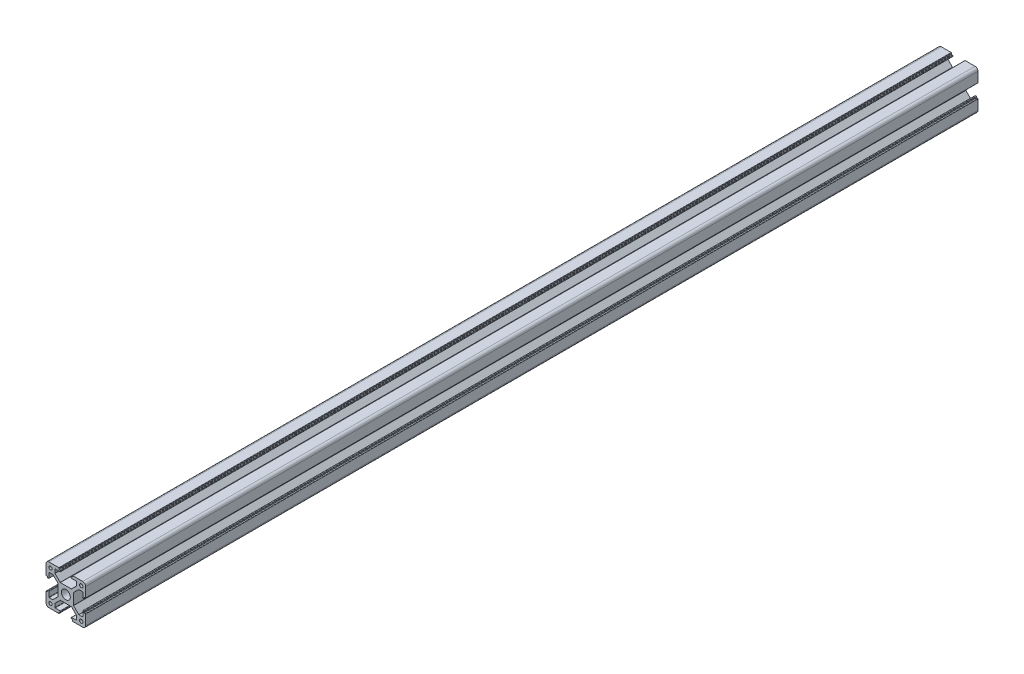
SolidWorks part; units mm, degrees
material "6063-T5"
ref_plane "Alzado" through (0, 0, 0) normal (0, 0, 1) x (1, 0, 0)
ref_plane "Planta" through (0, 0, 0) normal (0, 1, 0) x (1, 0, 0)
ref_plane "Vista lateral" through (0, 0, 0) normal (1, 0, 0) x (0, 0, -1)
sketch "Croquis1" plane through (0, 0, 0) normal (0, 0, 1) x (1, 0, 0)
  line L0 (0, 53.0989) -> (0, -48.4513) construction
  line L1 (-45.0818, 0) -> (46.476, 0) construction
  line L2 (-4.1615, 5.8) -> (4.1615, 5.8)
  line L3 (4.3029, 5.8586) -> (8.1914, 9.7471)
  line L4 (8.25, 9.8885) -> (8.25, 12.6)
  line L5 (8.05, 12.8) -> (4.3, 12.8)
  line L6 (4.1, 13) -> (4.1, 13.7)
  line L7 (4.3, 13.9) -> (4.9, 13.9)
  line L8 (5.1, 14.1) -> (5.1, 14.8)
  line L9 (5.3, 15) -> (12.8, 15)
  line L10 (0, 0) -> (45.9185, 45.9185) construction
  line L11 (15, 5.3) -> (15, 12.8)
  line L12 (13.9, 5.1) -> (14.8, 5.1)
  line L13 (13.9, 4.3) -> (13.9, 5.1)
  line L14 (13, 4.1) -> (13.7, 4.1)
  line L15 (12.8, 8.05) -> (12.8, 4.3)
  line L16 (9.8885, 8.25) -> (12.6, 8.25)
  line L17 (5.8586, 4.3029) -> (9.7471, 8.1914)
  line L18 (5.8, -4.1615) -> (5.8, 4.1615)
  line L19 (5.8586, -4.3029) -> (9.7471, -8.1914)
  line L20 (9.8885, -8.25) -> (12.6, -8.25)
  line L21 (12.8, -8.05) -> (12.8, -4.3)
  line L22 (13, -4.1) -> (13.7, -4.1)
  line L23 (13.9, -4.3) -> (13.9, -5.1)
  line L24 (13.9, -5.1) -> (14.8, -5.1)
  line L25 (15, -5.3) -> (15, -12.8)
  line L26 (5.3, -15) -> (12.8, -15)
  line L27 (5.1, -14.1) -> (5.1, -14.8)
  line L28 (4.3, -13.9) -> (4.9, -13.9)
  line L29 (4.1, -13) -> (4.1, -13.7)
  line L30 (8.05, -12.8) -> (4.3, -12.8)
  line L31 (8.25, -9.8885) -> (8.25, -12.6)
  line L32 (4.3029, -5.8586) -> (8.1914, -9.7471)
  line L33 (-4.1615, -5.8) -> (4.1615, -5.8)
  line L64 (-4.3029, -5.8586) -> (-8.1914, -9.7471)
  line L65 (-8.25, -9.8885) -> (-8.25, -12.6)
  line L66 (-8.05, -12.8) -> (-4.3, -12.8)
  line L67 (-4.1, -13) -> (-4.1, -13.7)
  line L68 (-4.3, -13.9) -> (-4.9, -13.9)
  line L69 (-5.1, -14.1) -> (-5.1, -14.8)
  line L70 (-5.3, -15) -> (-12.8, -15)
  line L71 (-15, -5.3) -> (-15, -12.8)
  line L72 (-13.9, -5.1) -> (-14.8, -5.1)
  line L73 (-13.9, -4.3) -> (-13.9, -5.1)
  line L74 (-13, -4.1) -> (-13.7, -4.1)
  line L75 (-12.8, -8.05) -> (-12.8, -4.3)
  line L76 (-9.8885, -8.25) -> (-12.6, -8.25)
  line L77 (-5.8586, -4.3029) -> (-9.7471, -8.1914)
  line L78 (-5.8586, 4.3029) -> (-9.7471, 8.1914)
  line L79 (-9.8885, 8.25) -> (-12.6, 8.25)
  line L80 (-12.8, 8.05) -> (-12.8, 4.3)
  line L81 (-13, 4.1) -> (-13.7, 4.1)
  line L82 (-13.9, 4.3) -> (-13.9, 5.1)
  line L83 (-13.9, 5.1) -> (-14.8, 5.1)
  line L84 (-15, 5.3) -> (-15, 12.8)
  line L85 (-5.3, 15) -> (-12.8, 15)
  line L86 (-5.1, 14.1) -> (-5.1, 14.8)
  line L87 (-4.3, 13.9) -> (-4.9, 13.9)
  line L88 (-4.1, 13) -> (-4.1, 13.7)
  line L89 (-8.05, 12.8) -> (-4.3, 12.8)
  line L90 (-8.25, 9.8885) -> (-8.25, 12.6)
  line L91 (-4.3029, 5.8586) -> (-8.1914, 9.7471)
  line L106 (-5.8, -4.1615) -> (-5.8, 4.1615)
  arc A0 (12.8, 15) -> (15, 12.8) centre (12.8, 12.8) cw
  arc A1 (5.1, 14.8) -> (5.3, 15) centre (5.3, 14.8) cw
  arc A2 (4.9, 13.9) -> (5.1, 14.1) centre (4.9, 14.1) ccw
  arc A3 (4.1, 13.7) -> (4.3, 13.9) centre (4.3, 13.7) cw
  arc A4 (4.3, 12.8) -> (4.1, 13) centre (4.3, 13) cw
  arc A5 (8.25, 12.6) -> (8.05, 12.8) centre (8.05, 12.6) ccw
  arc A6 (4.1615, 5.8) -> (4.3029, 5.8586) centre (4.1615, 6) ccw
  arc A7 (8.1914, 9.7471) -> (8.25, 9.8885) centre (8.05, 9.8885) ccw
  arc A8 (13, 4.1) -> (12.8, 4.3) centre (13, 4.3) cw
  arc A9 (5.8586, 4.3029) -> (5.8, 4.1615) centre (6, 4.1615) ccw
  arc A10 (9.8885, 8.25) -> (9.7471, 8.1914) centre (9.8885, 8.05) ccw
  arc A11 (12.8, 8.05) -> (12.6, 8.25) centre (12.6, 8.05) ccw
  arc A12 (13.9, 4.3) -> (13.7, 4.1) centre (13.7, 4.3) cw
  arc A13 (15, 5.3) -> (14.8, 5.1) centre (14.8, 5.3) cw
  arc A16 (15, -5.3) -> (14.8, -5.1) centre (14.8, -5.3) ccw
  arc A17 (13.9, -4.3) -> (13.7, -4.1) centre (13.7, -4.3) ccw
  arc A18 (12.8, -8.05) -> (12.6, -8.25) centre (12.6, -8.05) cw
  arc A19 (9.8885, -8.25) -> (9.7471, -8.1914) centre (9.8885, -8.05) cw
  arc A20 (5.8586, -4.3029) -> (5.8, -4.1615) centre (6, -4.1615) cw
  arc A21 (13, -4.1) -> (12.8, -4.3) centre (13, -4.3) ccw
  arc A22 (8.1914, -9.7471) -> (8.25, -9.8885) centre (8.05, -9.8885) cw
  arc A23 (4.1615, -5.8) -> (4.3029, -5.8586) centre (4.1615, -6) cw
  arc A24 (8.25, -12.6) -> (8.05, -12.8) centre (8.05, -12.6) cw
  arc A25 (4.3, -12.8) -> (4.1, -13) centre (4.3, -13) ccw
  arc A26 (4.1, -13.7) -> (4.3, -13.9) centre (4.3, -13.7) ccw
  arc A27 (4.9, -13.9) -> (5.1, -14.1) centre (4.9, -14.1) cw
  arc A28 (5.1, -14.8) -> (5.3, -15) centre (5.3, -14.8) ccw
  arc A29 (12.8, -15) -> (15, -12.8) centre (12.8, -12.8) ccw
  circle A44 centre (11.625, 11.625) radius 1.25
  circle A45 centre (11.625, -11.625) radius 1.25
  arc A60 (-12.8, -15) -> (-15, -12.8) centre (-12.8, -12.8) cw
  arc A61 (-5.1, -14.8) -> (-5.3, -15) centre (-5.3, -14.8) cw
  arc A62 (-4.9, -13.9) -> (-5.1, -14.1) centre (-4.9, -14.1) ccw
  arc A63 (-4.1, -13.7) -> (-4.3, -13.9) centre (-4.3, -13.7) cw
  arc A64 (-4.3, -12.8) -> (-4.1, -13) centre (-4.3, -13) cw
  arc A65 (-8.25, -12.6) -> (-8.05, -12.8) centre (-8.05, -12.6) ccw
  arc A66 (-4.1615, -5.8) -> (-4.3029, -5.8586) centre (-4.1615, -6) ccw
  arc A67 (-8.1914, -9.7471) -> (-8.25, -9.8885) centre (-8.05, -9.8885) ccw
  arc A68 (-13, -4.1) -> (-12.8, -4.3) centre (-13, -4.3) cw
  arc A69 (-5.8586, -4.3029) -> (-5.8, -4.1615) centre (-6, -4.1615) ccw
  arc A70 (-9.8885, -8.25) -> (-9.7471, -8.1914) centre (-9.8885, -8.05) ccw
  arc A71 (-12.8, -8.05) -> (-12.6, -8.25) centre (-12.6, -8.05) ccw
  arc A72 (-13.9, -4.3) -> (-13.7, -4.1) centre (-13.7, -4.3) cw
  arc A73 (-15, -5.3) -> (-14.8, -5.1) centre (-14.8, -5.3) cw
  arc A76 (-15, 5.3) -> (-14.8, 5.1) centre (-14.8, 5.3) ccw
  arc A77 (-13.9, 4.3) -> (-13.7, 4.1) centre (-13.7, 4.3) ccw
  arc A78 (-12.8, 8.05) -> (-12.6, 8.25) centre (-12.6, 8.05) cw
  arc A79 (-9.8885, 8.25) -> (-9.7471, 8.1914) centre (-9.8885, 8.05) cw
  arc A80 (-5.8586, 4.3029) -> (-5.8, 4.1615) centre (-6, 4.1615) cw
  arc A81 (-13, 4.1) -> (-12.8, 4.3) centre (-13, 4.3) ccw
  arc A82 (-8.1914, 9.7471) -> (-8.25, 9.8885) centre (-8.05, 9.8885) cw
  arc A83 (-4.1615, 5.8) -> (-4.3029, 5.8586) centre (-4.1615, 6) cw
  arc A84 (-8.25, 12.6) -> (-8.05, 12.8) centre (-8.05, 12.6) cw
  arc A85 (-4.3, 12.8) -> (-4.1, 13) centre (-4.3, 13) ccw
  arc A86 (-4.1, 13.7) -> (-4.3, 13.9) centre (-4.3, 13.7) ccw
  arc A87 (-4.9, 13.9) -> (-5.1, 14.1) centre (-4.9, 14.1) cw
  arc A88 (-5.1, 14.8) -> (-5.3, 15) centre (-5.3, 14.8) ccw
  arc A89 (-12.8, 15) -> (-15, 12.8) centre (-12.8, 12.8) ccw
  circle A104 centre (-11.625, -11.625) radius 1.25
  circle A105 centre (-11.625, 11.625) radius 1.25
  circle A120 centre (0, 0) radius 3.4
  point P5 (-15, -15)
  point P26 (15, 15)
  point P29 (5.1, 15)
  point P32 (5.1, 13.9)
  point P35 (4.1, 13.9)
  point P38 (4.1, 12.8)
  point P41 (8.25, 12.8)
  point P44 (4.2444, 5.8)
  point P47 (8.25, 9.8056)
  point P50 (12.8, 4.1)
  point P53 (5.8, 4.2444)
  point P56 (9.8056, 8.25)
  point P59 (12.8, 8.25)
  point P62 (13.9, 4.1)
  point P65 (15, 5.1)
  point P112 (5.8, 0)
  point P113 (0, 5.8)
  point P114 (15, -5.1)
  point P115 (13.9, -4.1)
  point P116 (12.8, -8.25)
  point P117 (9.8056, -8.25)
  point P118 (5.8, -4.2444)
  point P119 (12.8, -4.1)
  point P120 (8.25, -9.8056)
  point P121 (4.2444, -5.8)
  point P122 (8.25, -12.8)
  point P123 (4.1, -12.8)
  point P124 (4.1, -13.9)
  point P125 (5.1, -13.9)
  point P126 (5.1, -15)
  point P127 (15, -15)
  point P222 (0, -5.8)
  point P223 (-5.1, -15)
  point P224 (-5.1, -13.9)
  point P225 (-4.1, -13.9)
  point P226 (-4.1, -12.8)
  point P227 (-8.25, -12.8)
  point P228 (-4.2444, -5.8)
  point P229 (-8.25, -9.8056)
  point P230 (-12.8, -4.1)
  point P231 (-5.8, -4.2444)
  point P232 (-9.8056, -8.25)
  point P233 (-12.8, -8.25)
  point P234 (-13.9, -4.1)
  point P235 (-15, -5.1)
  point P236 (-5.8, 0)
  point P237 (-15, 5.1)
  point P238 (-13.9, 4.1)
  point P239 (-12.8, 8.25)
  point P240 (-9.8056, 8.25)
  point P241 (-5.8, 4.2444)
  point P242 (-12.8, 4.1)
  point P243 (-8.25, 9.8056)
  point P244 (-4.2444, 5.8)
  point P245 (-8.25, 12.8)
  point P246 (-4.1, 12.8)
  point P247 (-4.1, 13.9)
  point P248 (-5.1, 13.9)
  point P249 (-5.1, 15)
  point P250 (-15, 15)
  dimension "D8" = 2.2
  dimension "D9" = 0.2
  dimension "D12" = 6.8
  dimension "D1" = 2.2
  dimension "D2" = 8.25
  dimension "D3" = 15
  dimension "D4" = 9.2
  dimension "D5" = 4.1
  dimension "D6" = 5.1
  dimension "D7" = 2.2
  dimension "D11" = 3.375
extrude "Saliente-Extruir1" add sketch "Croquis1" along normal blind 675
